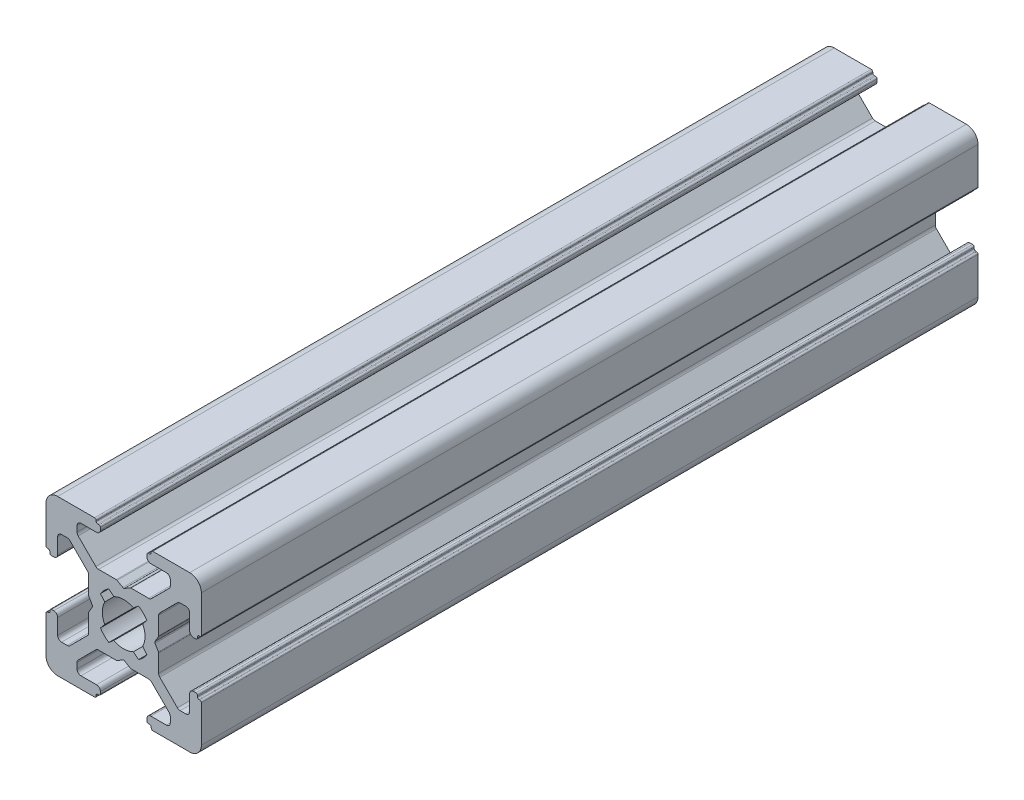
SolidWorks part; units mm, degrees
material "6061 Alloy"
ref_plane "Front Plane" through (0, 0, 0) normal (0, 0, 1) x (1, 0, 0)
ref_plane "Top Plane" through (0, 0, 0) normal (0, 1, 0) x (1, 0, 0)
ref_plane "Right Plane" through (0, 0, 0) normal (1, 0, 0) x (0, 0, -1)
sketch "Sketch1" plane through (0, 0, 0) normal (0, 0, 1) x (1, 0, 0)
  line L0 (0, 13.3675) -> (0, -10.9159) construction
  line L1 (-12.9725, 0) -> (15.1887, 0) construction
  line L2 (-3.5, 8.5) -> (-5.5, 8.5)
  line L3 (-3.55, 9.7) -> (-3.55, 9.8)
  line L4 (-6, 7.2678) -> (-6, 8)
  line L5 (-7.2678, 6) -> (-8, 6)
  line L6 (-3.75, 10) -> (-8.5, 10)
  line L7 (-9.7, 3.55) -> (-9.8, 3.55)
  line L8 (-9.5, 3.2) -> (-9.5, 3.35)
  line L9 (-9, 3) -> (-9.3, 3)
  line L10 (-4.4732, 0.8536) -> (-4.0381, 0.1)
  line L11 (-4.5, 3.2322) -> (-4.5, 0.9536)
  line L12 (-8.5, 3.5) -> (-8.5, 5.5)
  line L13 (-10, 3.75) -> (-10, 8.5)
  line L14 (-3.5858, 4.6464) -> (-5.8536, 6.9142)
  line L15 (-4.6464, 3.5858) -> (-6.9142, 5.8536)
  line L16 (-3.2, 9.5) -> (-3.35, 9.5)
  line L17 (-3, 9) -> (-3, 9.3)
  line L18 (-0.8536, 4.4732) -> (-0.1, 4.0381)
  line L19 (-3.2322, 4.5) -> (-0.9536, 4.5)
  line L20 (-1.2582, 2.4453) -> (-1.9139, 2.9896)
  line L21 (-2.4453, 1.2582) -> (-2.9922, 1.9099)
  line L22 (3.5, -8.5) -> (5.5, -8.5)
  line L23 (3.55, -9.7) -> (3.55, -9.8)
  line L24 (6, -7.2678) -> (6, -8)
  line L25 (7.2678, -6) -> (8, -6)
  line L26 (3.75, -10) -> (8.5, -10)
  line L27 (9.7, -3.55) -> (9.8, -3.55)
  line L28 (9.5, -3.2) -> (9.5, -3.35)
  line L29 (9, -3) -> (9.3, -3)
  line L30 (4.4732, -0.8536) -> (4.0381, -0.1)
  line L31 (4.5, -3.2322) -> (4.5, -0.9536)
  line L32 (8.5, -3.5) -> (8.5, -5.5)
  line L33 (10, -3.75) -> (10, -8.5)
  line L34 (3.5858, -4.6464) -> (5.8536, -6.9142)
  line L35 (4.6464, -3.5858) -> (6.9142, -5.8536)
  line L36 (3.2, -9.5) -> (3.35, -9.5)
  line L37 (3, -9) -> (3, -9.3)
  line L38 (0.8536, -4.4732) -> (0.1, -4.0381)
  line L39 (3.2322, -4.5) -> (0.9536, -4.5)
  line L40 (1.2582, -2.4453) -> (1.9139, -2.9896)
  line L41 (2.4453, -1.2582) -> (2.9922, -1.9099)
  line L42 (-2.4453, -1.2582) -> (-2.9922, -1.9099)
  line L43 (-1.2582, -2.4453) -> (-1.9139, -2.9896)
  line L44 (-3.2322, -4.5) -> (-0.9536, -4.5)
  line L45 (-0.8536, -4.4732) -> (-0.1, -4.0381)
  line L46 (-3, -9) -> (-3, -9.3)
  line L47 (-3.2, -9.5) -> (-3.35, -9.5)
  line L48 (-4.6464, -3.5858) -> (-6.9142, -5.8536)
  line L49 (-3.5858, -4.6464) -> (-5.8536, -6.9142)
  line L50 (-10, -3.75) -> (-10, -8.5)
  line L51 (-8.5, -3.5) -> (-8.5, -5.5)
  line L52 (-4.5, -3.2322) -> (-4.5, -0.9536)
  line L53 (-4.4732, -0.8536) -> (-4.0381, -0.1)
  line L54 (-9, -3) -> (-9.3, -3)
  line L55 (-9.5, -3.2) -> (-9.5, -3.35)
  line L56 (-9.7, -3.55) -> (-9.8, -3.55)
  line L57 (2.4453, 1.2582) -> (2.9922, 1.9099)
  line L58 (1.2582, 2.4453) -> (1.9139, 2.9896)
  line L59 (3.2322, 4.5) -> (0.9536, 4.5)
  line L60 (0.8536, 4.4732) -> (0.1, 4.0381)
  line L61 (-3.75, -10) -> (-8.5, -10)
  line L62 (-7.2678, -6) -> (-8, -6)
  line L63 (-6, -7.2678) -> (-6, -8)
  line L64 (3, 9) -> (3, 9.3)
  line L65 (3.2, 9.5) -> (3.35, 9.5)
  line L66 (4.6464, 3.5858) -> (6.9142, 5.8536)
  line L67 (3.5858, 4.6464) -> (5.8536, 6.9142)
  line L68 (10, 3.75) -> (10, 8.5)
  line L69 (8.5, 3.5) -> (8.5, 5.5)
  line L70 (4.5, 3.2322) -> (4.5, 0.9536)
  line L71 (4.4732, 0.8536) -> (4.0381, 0.1)
  line L72 (9, 3) -> (9.3, 3)
  line L73 (9.5, 3.2) -> (9.5, 3.35)
  line L74 (9.7, 3.55) -> (9.8, 3.55)
  line L75 (3.75, 10) -> (8.5, 10)
  line L76 (7.2678, 6) -> (8, 6)
  line L77 (6, 7.2678) -> (6, 8)
  line L78 (3.55, 9.7) -> (3.55, 9.8)
  line L79 (3.5, 8.5) -> (5.5, 8.5)
  line L80 (-3.55, -9.7) -> (-3.55, -9.8)
  line L81 (-3.5, -8.5) -> (-5.5, -8.5)
  arc A0 (-10, 8.5) -> (-8.5, 10) centre (-8.5, 8.5) cw
  arc A1 (-8.5, 5.5) -> (-8, 6) centre (-8, 5.5) cw
  arc A2 (-7.2678, 6) -> (-6.9142, 5.8536) centre (-7.2678, 5.5) cw
  arc A3 (-5.8536, 6.9142) -> (-6, 7.2678) centre (-5.5, 7.2678) cw
  arc A4 (-6, 8) -> (-5.5, 8.5) centre (-5.5, 8) cw
  arc A5 (-9.7, 3.55) -> (-9.5, 3.35) centre (-9.7, 3.35) cw
  arc A6 (-9.8, 3.55) -> (-10, 3.75) centre (-9.8, 3.75) cw
  arc A7 (-9.3, 3) -> (-9.5, 3.2) centre (-9.3, 3.2) cw
  arc A8 (-8.5, 3.5) -> (-9, 3) centre (-9, 3.5) cw
  arc A9 (-4.6464, 3.5858) -> (-4.5, 3.2322) centre (-5, 3.2322) cw
  arc A10 (-4.4732, 0.8536) -> (-4.5, 0.9536) centre (-4.3, 0.9536) cw
  arc A11 (-4.0381, 0.1) -> (-4.0381, -0.1) centre (-4.2113, 0) cw
  arc A12 (-3.2, 9.5) -> (-3, 9.3) centre (-3.2, 9.3) cw
  arc A13 (-0.9536, 4.5) -> (-0.8536, 4.4732) centre (-0.9536, 4.3) cw
  arc A14 (-2.9922, 1.9099) -> (-1.9139, 2.9896) centre (0, 0) cw
  arc A15 (-3.2322, 4.5) -> (-3.5858, 4.6464) centre (-3.2322, 5) cw
  arc A16 (-3.75, 10) -> (-3.55, 9.8) centre (-3.75, 9.8) cw
  arc A17 (-3.35, 9.5) -> (-3.55, 9.7) centre (-3.35, 9.7) cw
  arc A18 (2.4453, -1.2582) -> (2.4453, 1.2582) centre (0, 0) ccw
  arc A19 (-3, 9) -> (-3.5, 8.5) centre (-3.5, 9) cw
  arc A20 (-2.4453, -1.2582) -> (-2.4453, 1.2582) centre (0, 0) cw
  arc A21 (10, -8.5) -> (8.5, -10) centre (8.5, -8.5) cw
  arc A22 (8.5, -5.5) -> (8, -6) centre (8, -5.5) cw
  arc A23 (7.2678, -6) -> (6.9142, -5.8536) centre (7.2678, -5.5) cw
  arc A24 (5.8536, -6.9142) -> (6, -7.2678) centre (5.5, -7.2678) cw
  arc A25 (6, -8) -> (5.5, -8.5) centre (5.5, -8) cw
  arc A26 (9.7, -3.55) -> (9.5, -3.35) centre (9.7, -3.35) cw
  arc A27 (9.8, -3.55) -> (10, -3.75) centre (9.8, -3.75) cw
  arc A28 (9.3, -3) -> (9.5, -3.2) centre (9.3, -3.2) cw
  arc A29 (8.5, -3.5) -> (9, -3) centre (9, -3.5) cw
  arc A30 (4.6464, -3.5858) -> (4.5, -3.2322) centre (5, -3.2322) cw
  arc A31 (4.4732, -0.8536) -> (4.5, -0.9536) centre (4.3, -0.9536) cw
  arc A32 (3.2, -9.5) -> (3, -9.3) centre (3.2, -9.3) cw
  arc A33 (-0.1, -4.0381) -> (0.1, -4.0381) centre (0, -4.2113) cw
  arc A34 (0.9536, -4.5) -> (0.8536, -4.4732) centre (0.9536, -4.3) cw
  arc A35 (2.9922, -1.9099) -> (1.9139, -2.9896) centre (0, 0) cw
  arc A36 (1.2582, -2.4453) -> (-1.2582, -2.4453) centre (0, 0) cw
  arc A37 (3.2322, -4.5) -> (3.5858, -4.6464) centre (3.2322, -5) cw
  arc A38 (3.75, -10) -> (3.55, -9.8) centre (3.75, -9.8) cw
  arc A39 (3.35, -9.5) -> (3.55, -9.7) centre (3.35, -9.7) cw
  arc A40 (3, -9) -> (3.5, -8.5) centre (3.5, -9) cw
  arc A41 (-3, -9) -> (-3.5, -8.5) centre (-3.5, -9) ccw
  arc A42 (-3.35, -9.5) -> (-3.55, -9.7) centre (-3.35, -9.7) ccw
  arc A43 (-3.75, -10) -> (-3.55, -9.8) centre (-3.75, -9.8) ccw
  arc A44 (-3.2322, -4.5) -> (-3.5858, -4.6464) centre (-3.2322, -5) ccw
  arc A45 (-2.9922, -1.9099) -> (-1.9139, -2.9896) centre (0, 0) ccw
  arc A46 (-0.9536, -4.5) -> (-0.8536, -4.4732) centre (-0.9536, -4.3) ccw
  arc A47 (-3.2, -9.5) -> (-3, -9.3) centre (-3.2, -9.3) ccw
  arc A48 (-4.4732, -0.8536) -> (-4.5, -0.9536) centre (-4.3, -0.9536) ccw
  arc A49 (3, 9) -> (3.5, 8.5) centre (3.5, 9) ccw
  arc A50 (3.35, 9.5) -> (3.55, 9.7) centre (3.35, 9.7) ccw
  arc A51 (3.75, 10) -> (3.55, 9.8) centre (3.75, 9.8) ccw
  arc A52 (3.2322, 4.5) -> (3.5858, 4.6464) centre (3.2322, 5) ccw
  arc A53 (1.2582, 2.4453) -> (-1.2582, 2.4453) centre (0, 0) ccw
  arc A54 (-4.6464, -3.5858) -> (-4.5, -3.2322) centre (-5, -3.2322) ccw
  arc A55 (-8.5, -3.5) -> (-9, -3) centre (-9, -3.5) ccw
  arc A56 (-9.3, -3) -> (-9.5, -3.2) centre (-9.3, -3.2) ccw
  arc A57 (-9.8, -3.55) -> (-10, -3.75) centre (-9.8, -3.75) ccw
  arc A58 (-9.7, -3.55) -> (-9.5, -3.35) centre (-9.7, -3.35) ccw
  arc A59 (-6, -8) -> (-5.5, -8.5) centre (-5.5, -8) ccw
  arc A60 (2.9922, 1.9099) -> (1.9139, 2.9896) centre (0, 0) ccw
  arc A61 (0.9536, 4.5) -> (0.8536, 4.4732) centre (0.9536, 4.3) ccw
  arc A62 (-0.1, 4.0381) -> (0.1, 4.0381) centre (0, 4.2113) ccw
  arc A63 (-5.8536, -6.9142) -> (-6, -7.2678) centre (-5.5, -7.2678) ccw
  arc A64 (-7.2678, -6) -> (-6.9142, -5.8536) centre (-7.2678, -5.5) ccw
  arc A65 (-8.5, -5.5) -> (-8, -6) centre (-8, -5.5) ccw
  arc A66 (-10, -8.5) -> (-8.5, -10) centre (-8.5, -8.5) ccw
  arc A67 (3.2, 9.5) -> (3, 9.3) centre (3.2, 9.3) ccw
  arc A68 (4.0381, 0.1) -> (4.0381, -0.1) centre (4.2113, 0) ccw
  arc A69 (4.4732, 0.8536) -> (4.5, 0.9536) centre (4.3, 0.9536) ccw
  arc A70 (4.6464, 3.5858) -> (4.5, 3.2322) centre (5, 3.2322) ccw
  arc A71 (8.5, 3.5) -> (9, 3) centre (9, 3.5) ccw
  arc A72 (9.3, 3) -> (9.5, 3.2) centre (9.3, 3.2) ccw
  arc A73 (9.8, 3.55) -> (10, 3.75) centre (9.8, 3.75) ccw
  arc A74 (9.7, 3.55) -> (9.5, 3.35) centre (9.7, 3.35) ccw
  arc A75 (6, 8) -> (5.5, 8.5) centre (5.5, 8) ccw
  arc A76 (5.8536, 6.9142) -> (6, 7.2678) centre (5.5, 7.2678) ccw
  arc A77 (7.2678, 6) -> (6.9142, 5.8536) centre (7.2678, 5.5) ccw
  arc A78 (8.5, 5.5) -> (8, 6) centre (8, 5.5) ccw
  arc A79 (10, 8.5) -> (8.5, 10) centre (8.5, 8.5) ccw
  dimension "D4" = 5.5
  dimension "D1" = 6
  dimension "D2" = 20
  dimension "D3" = 20
  dimension "D5" = 5.5
  dimension "D6" = 10
  dimension "D7" = 6
  dimension "D8" = 6
  dimension "D9" = 6
extrude "Extrude1" add sketch "Sketch1" along normal blind 100
